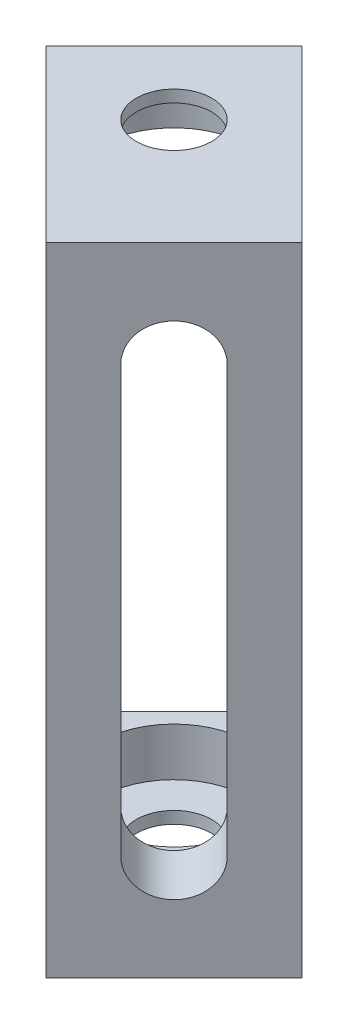
SolidWorks part; units mm, degrees
ref_plane "Front Plane" through (0, 0, 0) normal (0, 0, 1) x (1, 0, 0)
ref_plane "Top Plane" through (0, 0, 0) normal (0, 1, 0) x (1, 0, 0)
ref_plane "Right Plane" through (0, 0, 0) normal (1, 0, 0) x (0, 0, -1)
sketch "Sketch1" plane through (-67.7687, 0, -67.7687) normal (0.7071, 0, 0.7071) x (0.7071, 0, -0.7071)
  line L1 (-19.6398, 0) -> (-12.0198, 0)
  line L2 (-19.6398, 0) -> (-19.6398, 26.8542)
  line L3 (-19.6398, 26.8542) -> (-12.0198, 26.8542)
  line L4 (-12.0198, 0) -> (-12.0198, 26.8542)
  line L6 (-15.8298, 22.4092) -> (-15.8298, 4.445) construction
  line L7 (-14.2423, 22.4092) -> (-14.2423, 4.445)
  line L8 (-17.4173, 22.4092) -> (-17.4173, 4.445)
  line L9 (-15.8298, 26.8542) -> (-15.8298, 0) construction
  line L10 (-15.8298, 0) -> (-19.6398, 13.4271) construction
  line L11 (-19.6398, 13.4271) -> (-12.0198, 13.4271) construction
  arc A0 (-14.2423, 22.4092) -> (-17.4173, 22.4092) centre (-15.8298, 22.4092) ccw
  arc A1 (-17.4173, 4.445) -> (-14.2423, 4.445) centre (-15.8298, 4.445) ccw
  point P10 (-15.8298, 13.4271)
  point P15 (-15.9392, 13.4271)
  point P20 (-15.9392, 23.767)
  point P21 (0, 0)
  dimension "D1" = 3.175
  dimension "D2" = 7.62
  dimension "D3" = 4.445
extrude "Boss-Extrude1" add sketch "Sketch1" against normal blind 2.54
sketch "Sketch2" plane through (-69.5648, 0, -69.5648) normal (-0.7071, 0, -0.7071) x (-0.7071, 0, 0.7071)
  line L0 (19.6398, 26.8542) -> (19.6398, 0) construction
  line L1 (12.0198, 26.8542) -> (19.6398, 26.8542)
  line L2 (12.0198, 26.8542) -> (12.0198, 24.3142)
  line L3 (12.0198, 24.3142) -> (19.6398, 24.3142)
  line L4 (19.6398, 26.8542) -> (19.6398, 24.3142)
  line L6 (12.0198, 0) -> (19.6398, 0)
  line L7 (12.0198, 0) -> (12.0198, 2.54)
  line L8 (12.0198, 2.54) -> (19.6398, 2.54)
  line L9 (19.6398, 0) -> (19.6398, 2.54)
  dimension "D1" = 2.54
extrude "Boss-Extrude2" add sketch "Sketch2" along normal blind 7.62
sketch "Sketch3" [suppressed] plane through (0, 2.54, 0) normal (0, 1, 0) x (1, 0, 0)
  line L0 (24.716, -32.5163) -> (20.906, -47.1026) construction
  line L3 (20.906, -47.1026) -> (24.716, -43.2926) construction
  line L5 (24.716, -43.2926) -> (17.096, -43.2926) construction
  line L7 (20.1169, -47.8917) -> (25.505, -42.5035) construction
  line L8 (20.1169, -37.1154) -> (25.505, -42.5035) construction
  point P2 (22.811, -45.1976)
  point P5 (22.811, -39.8095)
sketch "Sketch4" [suppressed] plane through (0, 24.3142, 0) normal (0, -1, 0) x (1, 0, 0)
  line L0 (-12.0198, 77.2704) -> (-19.6398, 77.2704) construction
  line L1 (20.1169, 37.1154) -> (25.505, 42.5035) construction
  line L2 (14.7287, 42.5035) -> (20.1169, 47.8917) construction
  line L3 (-19.6398, 77.2704) -> (-15.8298, 73.4604) construction
  line L4 (20.1169, 37.1154) -> (14.7287, 42.5035) construction
  line L5 (-15.8298, 73.4604) -> (-15.8298, 81.0804) construction
  line L6 (25.505, 42.5035) -> (20.1169, 47.8917) construction
hole_wizard "CBORE for #4 Binding Head Machine Screw1" [suppressed] positions "Sketch5" profile "Sketch6" counterbore size "#4" standard "ANSI Inch"
sketch "Sketch5" [suppressed] plane through (0, 24.3142, 0) normal (0, -1, 0) x (-1, 0, 0)
  line L0 (15.8298, -73.4604) -> (15.8298, -81.0804) construction
  line L1 (12.0198, -77.2704) -> (19.6398, -77.2704) construction
  point P0 (15.8298, -77.2704)
  point P3 (15.8904, -76.2522)
sketch "Sketch6" plane through (-15.8298, 24.3142, 77.2704) normal (1, 0, 0) x (0, 0, -1)
  line L0 (0, 0) -> (0, 2.54)
  line L1 (0, 2.54) -> (1.5875, 2.54)
  line L3 (1.5875, 2.54) -> (1.5875, 2.032)
  line L4 (1.5875, 2.032) -> (3.175, 2.032)
  line L5 (3.175, 2.032) -> (3.175, 0)
  line L7 (3.175, 0) -> (0, 0)
  line L11 (0, -6.35) -> (0, 107.95) construction
  dimension "Thru Hole Dia." = 3.175
  dimension "Thru Hole Depth" = 2.54
  dimension "C'Bore Dia." = 6.35
  dimension "C'Bore Depth" = 2.032
hole_wizard "CBORE for #4 Binding Head Machine Screw2" [suppressed] positions "Sketch7" profile "Sketch8" counterbore size "#4" standard "ANSI Inch"
sketch "Sketch7" [suppressed] plane through (0, 2.54, 0) normal (0, 1, 0) x (1, 0, 0)
  line L0 (24.716, -32.5163) -> (20.906, -47.1026) construction
  line L1 (24.716, -43.2926) -> (17.096, -43.2926) construction
  point P0 (21.9011, -43.2926)
  point P3 (-15.8168, -75.9129)
sketch "Sketch8" plane through (21.9011, 2.54, 43.2926) normal (1, 0, 0) x (0, 0, 1)
  line L0 (0, 0) -> (0, 2.54)
  line L1 (0, 2.54) -> (1.5875, 2.54)
  line L3 (1.5875, 2.54) -> (1.5875, 2.032)
  line L4 (1.5875, 2.032) -> (3.175, 2.032)
  line L5 (3.175, 2.032) -> (3.175, 0)
  line L7 (3.175, 0) -> (0, 0)
  line L11 (0, -6.35) -> (0, 107.95) construction
  dimension "Thru Hole Dia." = 3.175
  dimension "Thru Hole Depth" = 2.54
  dimension "C'Bore Dia." = 6.35
  dimension "C'Bore Depth" = 2.032
sketch "Sketch9" plane through (0, 24.3142, 0) normal (0, -1, 0) x (1, 0, 0)
  line L0 (-86.1462, -58.3714) -> (-80.7581, -63.7596) construction
  line L1 (-88.8403, -61.0655) -> (-83.4522, -55.6773) construction
  line L2 (-83.4522, -66.4537) -> (-78.064, -61.0655) construction
  line L3 (-80.7581, -63.7596) -> (-86.1462, -63.7596) construction
  line L4 (-83.4522, -66.4537) -> (-88.8403, -61.0655) construction
  line L5 (-86.1462, -63.7596) -> (-80.7581, -58.3714) construction
  line L6 (-78.064, -61.0655) -> (-83.4522, -55.6773) construction
sketch "Sketch10" plane through (0, 2.54, 0) normal (0, 1, 0) x (1, 0, 0)
  line L0 (-86.1462, 58.3714) -> (-80.7581, 63.7596) construction
  line L1 (-88.8403, 61.0655) -> (-83.4522, 55.6773) construction
  line L2 (-83.4522, 66.4537) -> (-78.064, 61.0655) construction
  line L3 (-80.7581, 63.7596) -> (-80.7581, 58.3714) construction
  line L4 (-83.4522, 55.6773) -> (-78.064, 61.0655) construction
  line L5 (-80.7581, 58.3714) -> (-86.1462, 63.7596) construction
  line L6 (-88.8403, 61.0655) -> (-83.4522, 66.4537) construction
hole_wizard "CBORE for #4 Binding Head Machine Screw3" positions "Sketch11" profile "Sketch12" counterbore size "#4" standard "ANSI Inch"
sketch "Sketch11" plane through (0, 2.54, 0) normal (0, 1, 0) x (1, 0, 0)
  line L0 (-86.1462, 58.3714) -> (-80.7581, 63.7596) construction
  line L1 (-80.7581, 58.3714) -> (-86.1462, 63.7596) construction
  point P0 (-83.4522, 61.0655)
sketch "Sketch12" plane through (-83.4522, 2.54, -61.0655) normal (1, 0, 0) x (0, 0, 1)
  line L0 (0, 0) -> (0, 2.54)
  line L1 (0, 2.54) -> (1.5875, 2.54)
  line L3 (1.5875, 2.54) -> (1.5875, 2.032)
  line L4 (1.5875, 2.032) -> (3.175, 2.032)
  line L5 (3.175, 2.032) -> (3.175, 0)
  line L7 (3.175, 0) -> (0, 0)
  line L11 (0, -6.35) -> (0, 107.95) construction
  dimension "Thru Hole Dia." = 3.175
  dimension "Thru Hole Depth" = 2.54
  dimension "C'Bore Dia." = 6.35
  dimension "C'Bore Depth" = 2.032
hole_wizard "CBORE for #4 Binding Head Machine Screw4" positions "Sketch13" profile "Sketch14" counterbore size "#4" standard "ANSI Inch"
sketch "Sketch13" plane through (0, 24.3142, 0) normal (0, -1, 0) x (-1, 0, 0)
  line L0 (86.1462, 63.7596) -> (80.7581, 58.3714) construction
  line L1 (86.1462, 58.3714) -> (80.7581, 63.7596) construction
  point P0 (83.4522, 61.0655)
sketch "Sketch14" plane through (-83.4522, 24.3142, -61.0655) normal (1, 0, 0) x (0, 0, -1)
  line L0 (0, 0) -> (0, 2.54)
  line L1 (0, 2.54) -> (1.5875, 2.54)
  line L3 (1.5875, 2.54) -> (1.5875, 2.032)
  line L4 (1.5875, 2.032) -> (3.175, 2.032)
  line L5 (3.175, 2.032) -> (3.175, 0)
  line L7 (3.175, 0) -> (0, 0)
  line L11 (0, -6.35) -> (0, 107.95) construction
  dimension "Thru Hole Dia." = 3.175
  dimension "Thru Hole Depth" = 2.54
  dimension "C'Bore Dia." = 6.35
  dimension "C'Bore Depth" = 2.032
